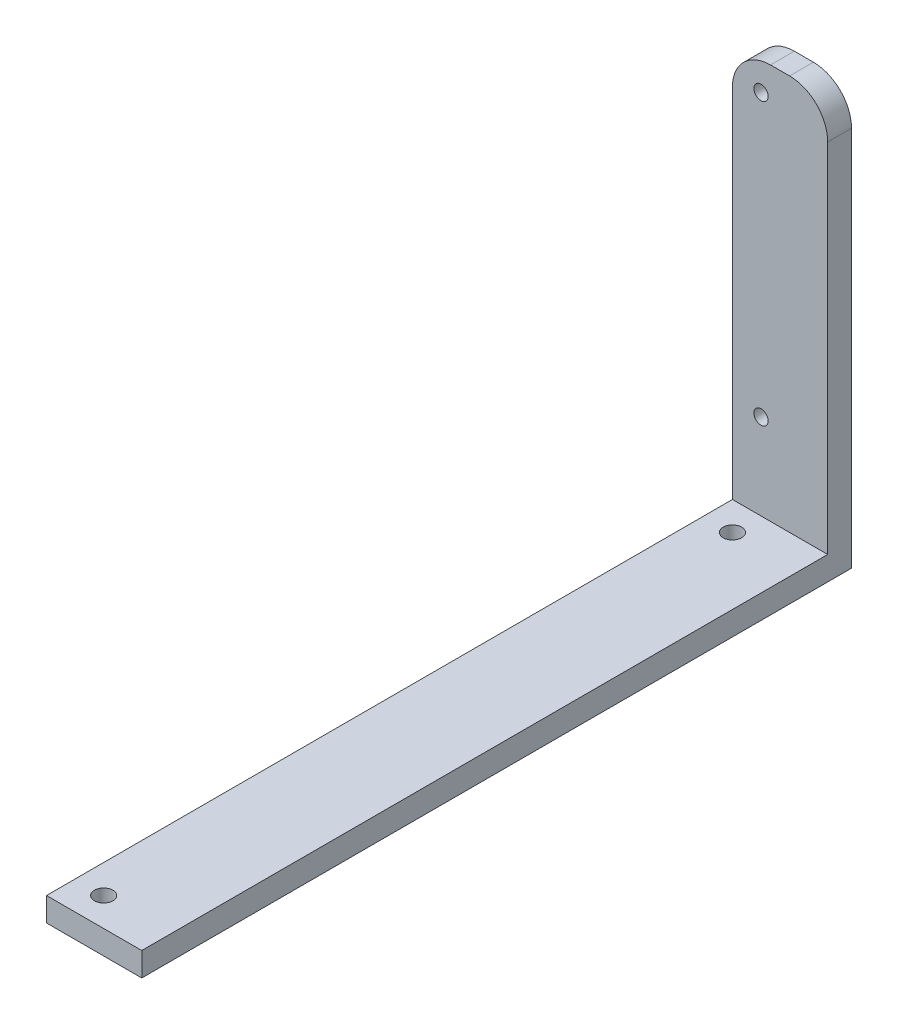
SolidWorks part; units mm, degrees
ref_plane "Front Plane" through (0, 0, 0) normal (0, 0, 1) x (1, 0, 0)
ref_plane "Top Plane" through (0, 0, 0) normal (0, 1, 0) x (1, 0, 0)
ref_plane "Right Plane" through (0, 0, 0) normal (1, 0, 0) x (0, 0, -1)
sketch "Sketch1" plane through (0, 0, 0) normal (0, 0, 1) x (1, 0, 0)
  line L1 (0, 0) -> (20, 0)
  line L2 (0, 0) -> (0, 88)
  line L3 (0, 88) -> (20, 88)
  line L4 (20, 0) -> (20, 88)
  circle A0 centre (6, 82) radius 1.5
  circle A1 centre (6, 23) radius 1.5
  dimension "D3" = 3
  dimension "D1" = 88
  dimension "D2" = 20
  dimension "D4" = 6
  dimension "D5" = 6
  dimension "D6" = 59
extrude "Boss-Extrude1" add sketch "Sketch1" along normal blind 5
sketch "Sketch2" plane through (0, 0, 5) normal (0, 0, 1) x (1, 0, 0)
  line L0 (20, 0) -> (20, 88) construction
  line L1 (0, 0) -> (20, 0)
  line L2 (0, 0) -> (0, 5)
  line L3 (0, 5) -> (20, 5)
  line L4 (20, 0) -> (20, 5)
  dimension "D1" = 5
extrude "Boss-Extrude2" add sketch "Sketch2" along normal blind 144
fillet "Fillet1" radius 8 2 edges at (20, 88, 2.5) (0, 88, 2.5)
sketch "Sketch3" plane through (0, 5, 0) normal (0, 1, 0) x (1, 0, 0)
  line L0 (20, -149) -> (0, -149) construction
  line L1 (20, -5) -> (0, -5) construction
  line L2 (0, -149) -> (0, -5) construction
  circle A0 centre (6, -143) radius 1.9394
  circle A1 centre (6, -11) radius 1.9394
  dimension "D1" = 6
  dimension "D2" = 6
  dimension "D3" = 6
extrude "Cut-Extrude1" cut sketch "Sketch3" against normal through all
